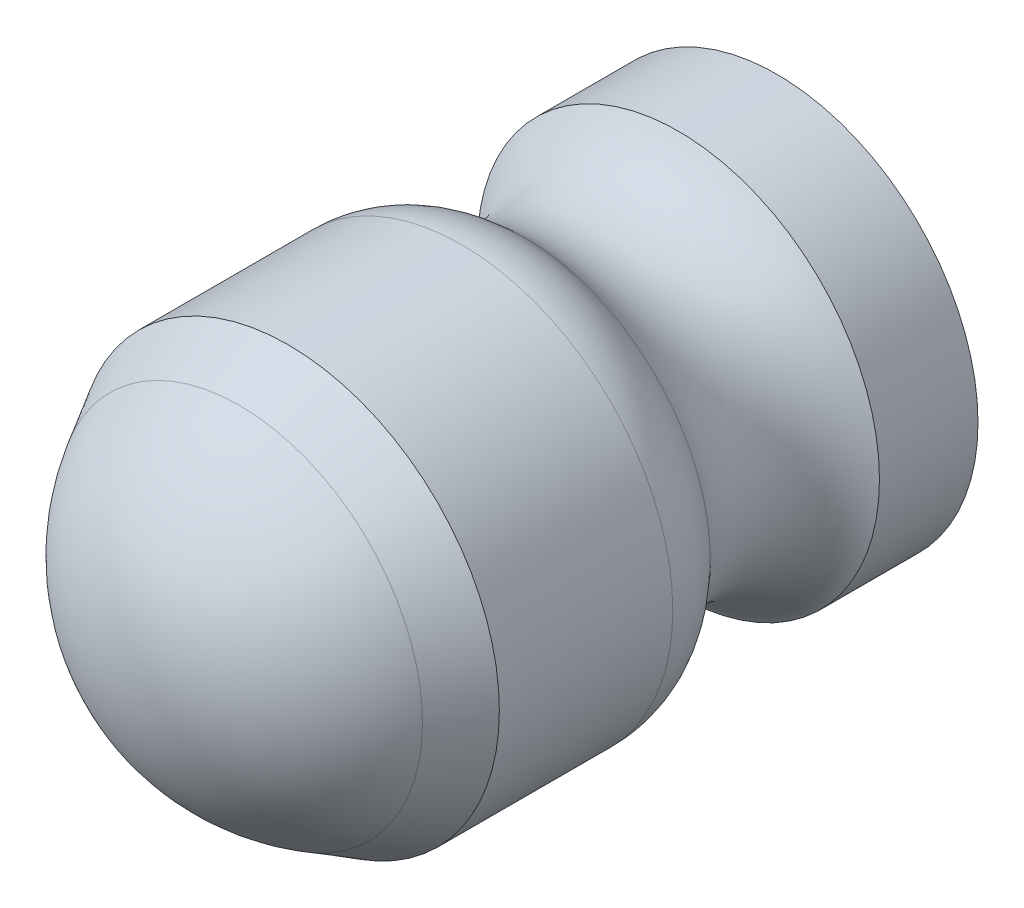
SolidWorks part; units mm, degrees
ref_plane "Alzado" through (0, 0, 0) normal (0, 0, 1) x (1, 0, 0)
ref_plane "Planta" through (0, 0, 0) normal (0, 1, 0) x (1, 0, 0)
ref_plane "Vista lateral" through (0, 0, 0) normal (1, 0, 0) x (0, 0, -1)
sketch "Croquis1" plane through (0, 0, 0) normal (0, 0, 1) x (1, 0, 0)
  circle A0 centre (0, 0) radius 10.5
  dimension "D1" = 21
extrude "Saliente-Extruir1" add sketch "Croquis1" along normal blind 8
sketch "Croquis3" plane through (0, 0, 0) normal (1, 0, 0) x (0, 0, -1)
  line L0 (0, 0) -> (-5.2, 0) construction
  line L1 (-8, 10.5) -> (-8, -10.5) construction
  line L2 (-5.2, 0) -> (-8, 0) construction
  line L3 (-8, 0) -> (-15.7, 0) construction
  line L4 (-8, 10.5) -> (-10.4282, 9.1058)
  line L5 (-8, 10.5) -> (-8, 0)
  line L6 (-8, 0) -> (-15.7, 0)
  arc A0 (-10.4282, 9.1058) -> (-15.7, 0) centre (-5.2, 0) ccw
  dimension "D1" = 21
  dimension "D2" = 7.7
revolve "Revolución1" add sketch "Croquis3" angle 360 about L6
sketch "Croquis4" plane through (0, 0, 0) normal (1, 0, 0) x (0, 0, -1)
  line L0 (0, 0) -> (18.122, 0) construction
  line L1 (0, 0) -> (0, 10.5)
  line L2 (0, 10.5) -> (0.6235, 10.5)
  line L3 (0, 0) -> (16.3, 0)
  line L6 (11.4, 10) -> (16.3, 10)
  line L7 (16.3, 10) -> (16.3, 0)
  arc A0 (3.766, 9.2211) -> (11.4, 10) centre (7.2575, 12.8) ccw
  arc A1 (3.766, 9.2211) -> (0.6235, 10.5) centre (0.6235, 6) ccw
  dimension "D1" = 16.3
  dimension "D5" = 20
revolve "Revolución2" add sketch "Croquis4" angle 360 about L0
sketch "Croquis5" plane through (0, 0, -16.3) normal (0, 0, -1) x (-1, 0, 0)
  circle A0 centre (0, 0) radius 3
  dimension "D1" = 6
extrude "Cortar-Extruir1" cut sketch "Croquis5" against normal blind 15
